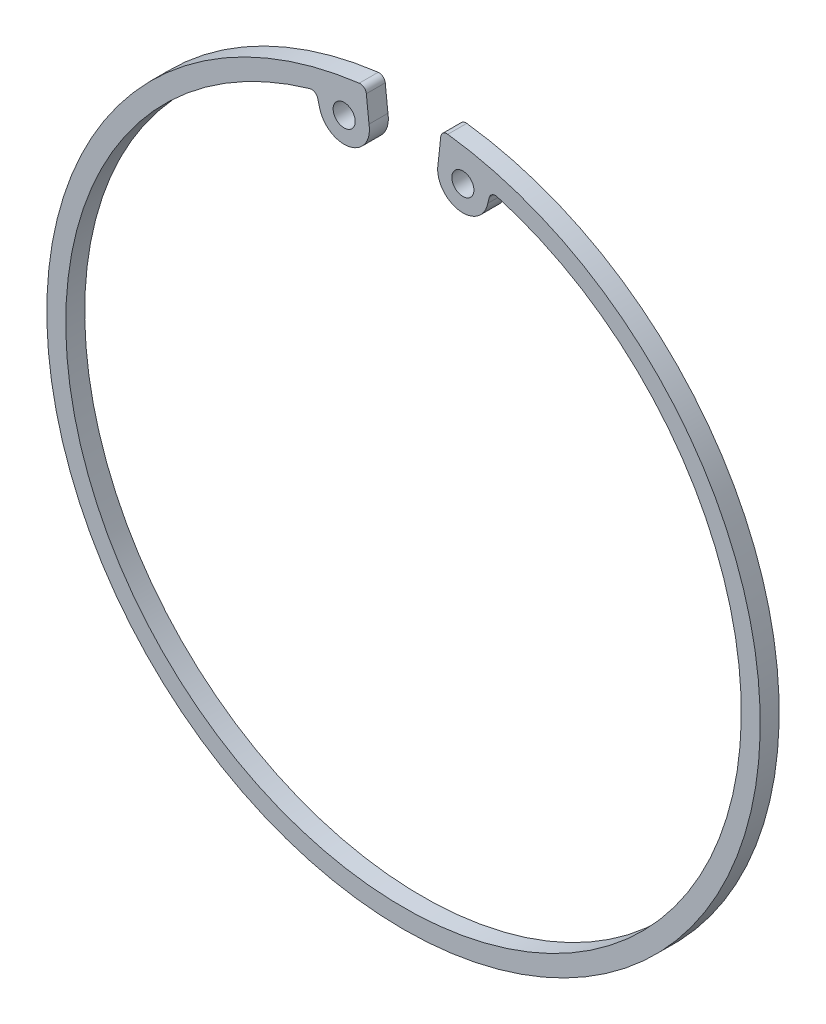
SolidWorks part; units mm, degrees
material "1.0301 (C10)"
ref_plane "Piano frontale" through (0, 0, 0) normal (0, 0, 1) x (1, 0, 0)
ref_plane "Piano superiore" through (0, 0, 0) normal (0, 1, 0) x (1, 0, 0)
ref_plane "Piano destro" through (0, 0, 0) normal (1, 0, 0) x (0, 0, -1)
sketch "Schizzo1" plane through (0, 0, 0) normal (0, 0, 1) x (1, 0, 0)
  line L2 (-5.8928, 55.1772) -> (-5.5742, 52.1937)
  line L9 (5.8928, 55.1772) -> (5.5742, 52.1937)
  line L10 (-5.5742, 52.1937) -> (-5.469, 51.2088)
  line L11 (5.5742, 52.1937) -> (5.469, 51.2088)
  line L12 (-13.5902, 50.7007) -> (-13.3338, 49.7439)
  line L13 (13.5902, 50.7007) -> (13.3338, 49.7439)
  line L14 (-13.3338, 49.7439) -> (-5.469, 51.2088) construction
  line L15 (5.469, 51.2088) -> (13.3338, 49.7439) construction
  arc A4 (-7.0113, 56.0633) -> (7.0113, 56.0633) centre (0, 0) ccw
  arc A5 (-14.8334, 51.4025) -> (14.8334, 51.4025) centre (0, 0) ccw
  arc A7 (-13.3338, 49.7439) -> (-5.469, 51.2088) centre (-9.4014, 50.4764) ccw
  arc A8 (5.469, 51.2088) -> (13.3338, 49.7439) centre (9.4014, 50.4764) ccw
  circle A9 centre (-9.4014, 50.4764) radius 1.75
  circle A10 centre (9.4014, 50.4764) radius 1.75
  arc A11 (13.5902, 50.7007) -> (14.8334, 51.4025) centre (14.5561, 50.4417) cw
  arc A12 (5.8928, 55.1772) -> (7.0113, 56.0633) centre (6.8872, 55.071) cw
  arc A13 (-13.5902, 50.7007) -> (-14.8334, 51.4025) centre (-14.5561, 50.4417) ccw
  arc A14 (-5.8928, 55.1772) -> (-7.0113, 56.0633) centre (-6.8872, 55.071) ccw
  point P19 (6, 56.1805)
  point P22 (-13.8516, 51.6758)
  point P26 (-6, 56.1805)
  dimension "D1" = 113
  dimension "D2" = 107
  dimension "D6" = 13.8516
  dimension "D7" = 3.5
  dimension "D3" = 6
  dimension "D8" = 1
  dimension "D4" = 8
  dimension "D5" = 5
extrude "Estrusione-Estrusione1" add sketch "Schizzo1" along normal blind 3
